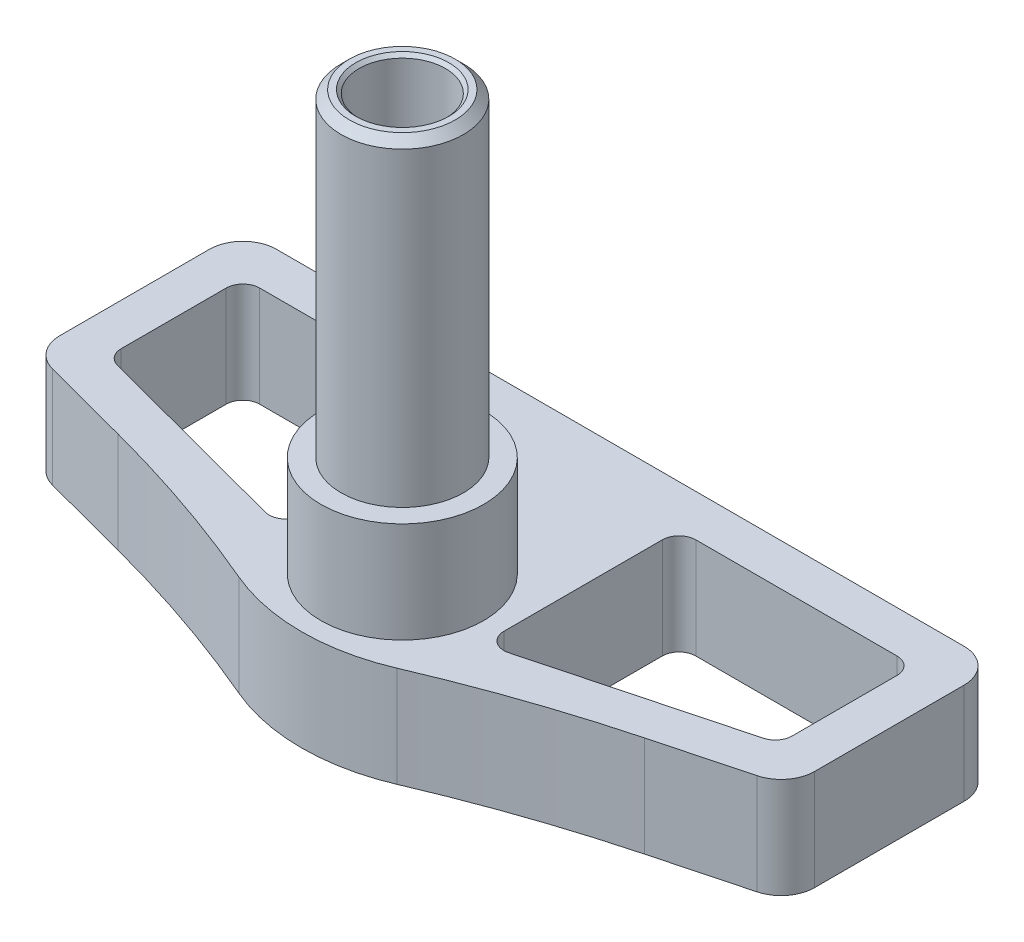
SolidWorks part; units mm, degrees
ref_plane "Front Plane" through (0, 0, 0) normal (0, 0, 1) x (1, 0, 0)
ref_plane "Top Plane" through (0, 0, 0) normal (0, 1, 0) x (1, 0, 0)
ref_plane "Right Plane" through (0, 0, 0) normal (1, 0, 0) x (0, 0, -1)
sketch "Sketch2" plane through (0, 0, 0) normal (0, 0, 1) x (1, 0, 0)
  line L1 (-12.5, 60) -> (12.5, 60)
  line L2 (-12.5, 60) -> (-12.5, 10)
  line L3 (-12.5, 10) -> (12.5, 10)
  line L4 (12.5, 60) -> (12.5, 10)
  line L5 (-22.5, 70) -> (22.5, 70)
  line L6 (-22.5, 70) -> (-22.5, 0)
  line L7 (-22.5, 0) -> (22.5, 0)
  line L8 (22.5, 70) -> (22.5, 0)
  point P4 (0, 10)
  point P10 (0, 0)
  dimension "D1" = 60
  dimension "D2" = 25
  dimension "D3" = 10
  dimension "D4" = 10
  dimension "D5" = 10
extrude "Boss-Extrude2" add sketch "Sketch2" along normal blind 10
sketch "Sketch3" plane through (0, 70, 0) normal (0, 1, 0) x (1, 0, 0)
  line L0 (-12, 0) -> (-12, -4)
  line L1 (22.5, 0) -> (-22.5, 0) construction
  line L2 (-12, -4) -> (-5, -4)
  line L3 (-5, -4) -> (-5, -8)
  line L4 (-5, -8) -> (5, -8)
  line L5 (5, -8) -> (5, -4)
  line L6 (5, -4) -> (12, -4)
  line L7 (12, -4) -> (12, 0)
  line L8 (-12, 0) -> (12, 0)
  point P4 (0, -8)
  dimension "D1" = 8
  dimension "D2" = 4
  dimension "D3" = 10
  dimension "D4" = 24
extrude "Cut-Extrude1" cut sketch "Sketch3" against normal up to next
sketch "Sketch4" plane through (0, 70, 0) normal (0, 1, 0) x (1, 0, 0)
  line L0 (-12, -10) -> (12, -10)
  line L1 (22.5, -10) -> (-22.5, -10) construction
  arc A0 (12, -10) -> (4.8, -15.4) centre (12, -17.5) ccw
  arc A1 (4.8, -15.4) -> (-4.8, -15.4) centre (0, -14) cw
  arc A2 (-4.8, -15.4) -> (-12, -10) centre (-12, -17.5) ccw
  circle A3 centre (0, -14) radius 3.65 construction
  dimension "D1" = 7.3
  dimension "D4" = 5
  dimension "D2" = 14
  dimension "D3" = 7.5
extrude "Boss-Extrude3" add sketch "Sketch4" against normal up to surface (10 mm away) up to face at (0, 60, 4.3333)
sketch "Sketch6" plane through (0, 70, 0) normal (0, 1, 0) x (1, 0, 0)
  circle A0 centre (0, -13) radius 3.65
  circle A1 centre (0, -13) radius 4.85 construction
  dimension "D1" = 7.3
  dimension "D2" = 9.7
  dimension "D3" = 13
extrude "Boss-Extrude4" add sketch "Sketch6" along normal blind 16
sketch "Sketch7" plane through (0, 0, 0) normal (0, -1, 0) x (1, 0, 0)
  line L1 (63, 1.7311) -> (15.6931, 14.2587) construction
  line L2 (-15.6931, 14.2587) -> (-63, 1.7311) construction
  line L3 (63, 1.7311) -> (15.6931, 14.2587) construction
  line L4 (-15.6931, 14.2587) -> (-63, 1.7311) construction
  line L5 (-22.5, 10) -> (-22.5, 12.4561)
  line L6 (-22.5, 12.4561) -> (-15.6931, 14.2587)
  line L7 (15.6931, 14.2587) -> (22.5, 12.4561)
  line L8 (22.5, 12.4561) -> (22.5, 10)
  line L9 (22.5, 10) -> (-22.5, 10)
  arc A6 (12.8214, 17.2181) -> (15.6931, 14.2587) centre (16.7171, 18.1254) ccw construction
  arc A7 (-15.6931, 14.2587) -> (-12.8214, 17.2181) centre (-16.7171, 18.1254) ccw construction
  arc A8 (12.8214, 17.2181) -> (15.6931, 14.2587) centre (16.7171, 18.1254) ccw construction
  arc A9 (-15.6931, 14.2587) -> (-12.8214, 17.2181) centre (-16.7171, 18.1254) ccw construction
  arc A11 (-15.6931, 14.2587) -> (-4.7143, 18.0352) centre (-36.2283, 91.8038) ccw
  arc A12 (-4.7143, 18.0352) -> (4.7143, 18.0352) centre (0, 7) cw
  arc A13 (4.7143, 18.0352) -> (15.6931, 14.2587) centre (36.2283, 91.8038) ccw
  dimension "D2" = 12
  dimension "D1" = 7
extrude "Boss-Extrude5" add sketch "Sketch7" against normal up to surface (10 mm away) up to face at (0, 10, 5)
sketch "Sketch8" plane through (0, 0, 0) normal (1, 0, 0) x (0, 0, -1)
  line L0 (-19, 70) -> (-19, 66.9) construction
  line L1 (-15.4, 70) -> (-19, 70) construction
  line L2 (-19, 60) -> (-19, 50.5) construction
  line L3 (-19, 60) -> (-15.4, 60) construction
  line L4 (-19, 66.9) -> (-23, 66.9)
  line L5 (-23, 66.9) -> (-23, 50.5)
  line L6 (-23, 50.5) -> (-19.5, 50.5)
  line L7 (-19.5, 50.5) -> (-10, 60)
  line L8 (-19, 70) -> (-19, 60) construction
  line L11 (-19, 66.9) -> (-10, 66.9)
  line L12 (-10, 60) -> (-10, 70) construction
  line L13 (-10, 66.9) -> (-10, 60)
  dimension "D1" = 9.5
  dimension "D2" = 3.1
  dimension "D3" = 45
  dimension "D5" = 4
extrude "Boss-Extrude8" add sketch "Sketch8" along normal mid plane 16
sketch "Sketch9" plane through (0, 0, 23) normal (0, 0, 1) x (1, 0, 0)
  line L0 (8, 66.9) -> (-8, 66.9) construction
  line L1 (-3, 66.9) -> (3, 66.9)
  line L2 (-3, 66.9) -> (-3, 50.5)
  line L3 (-3, 50.5) -> (3, 50.5)
  line L4 (3, 66.9) -> (3, 50.5)
  line L5 (8, 50.5) -> (-8, 50.5) construction
  point P8 (0, 50.5)
  dimension "D1" = 6
extrude "Cut-Extrude2" cut sketch "Sketch9" against normal blind 6
sketch "Sketch10" plane through (-8, 0, 0) normal (-1, 0, 0) x (0, 0, 1)
  line L0 (23, 50.5) -> (23, 66.9) construction
  line L1 (19.5, 50.5) -> (17, 53) construction
  line L2 (17, 53) -> (17, 66.9) construction
  line L3 (23, 50.5) -> (23, 66.9) construction
  line L4 (19.5, 50.5) -> (17, 53) construction
  line L5 (17, 53) -> (17, 66.9) construction
  line L6 (18.35, 64.4) -> (18.35, 54.4)
  line L7 (21.65, 54.4) -> (21.65, 64.4)
  line L8 (17, 59.95) -> (23, 59.95) construction
  line L9 (11.1557, 66.9) -> (23, 66.9) construction
  arc A0 (18.35, 54.4) -> (21.65, 54.4) centre (20, 54.4) ccw
  arc A1 (21.65, 64.4) -> (18.35, 64.4) centre (20, 64.4) ccw
  point P14 (20, 59.95)
  dimension "D1" = 3.3
  dimension "D2" = 10
  dimension "D3" = 2.5
extrude "Cut-Extrude3" cut sketch "Sketch10" against normal through all both and the other way through all
sketch "Sketch11" plane through (0, 10, 0) normal (0, 1, 0) x (1, 0, 0)
  line L1 (-32.1748, 6.5469) -> (31.625, 6.5469)
  line L2 (-32.1748, 6.5469) -> (-32.1748, -25.2398)
  line L3 (-32.1748, -25.2398) -> (31.625, -25.2398)
  line L4 (31.625, 6.5469) -> (31.625, -25.2398)
extrude "Cut-Extrude4" cut sketch "Sketch11" along normal through all
sketch "Sketch12" plane through (0, 10, 0) normal (0, 1, 0) x (1, 0, 0)
  circle A1 centre (0, -13) radius 3.65
  circle A2 centre (0, -13) radius 3.65
  dimension "D1" = 0
extrude "Boss-Extrude9" add sketch "Sketch12" along normal blind 21
sketch "Sketch13" plane through (0, 10, 0) normal (0, 1, 0) x (1, 0, 0)
  circle A0 centre (0, -13) radius 4.85
  circle A3 centre (0, -13) radius 3.65 construction
  circle A4 centre (0, -13) radius 3.65
  dimension "D2" = 9.7
extrude "Boss-Extrude10" add sketch "Sketch13" along normal blind 2
sketch "Sketch14" plane through (0, 10, 0) normal (0, 1, 0) x (1, 0, 0)
  line L5 (22.5, -12.4561) -> (22.5, 0)
  line L6 (22.5, 0) -> (-22.5, 0)
  line L7 (-22.5, 0) -> (-22.5, -12.4561)
  line L8 (-22.5, -12.4561) -> (-15.6931, -14.2587)
  line L9 (15.6931, -14.2587) -> (22.5, -12.4561)
  line L10 (22.5, -12.4561) -> (22.5, 0)
  line L11 (22.5, 0) -> (-22.5, 0)
  line L12 (-22.5, 0) -> (-22.5, -12.4561)
  line L13 (-22.5, -12.4561) -> (-15.6931, -14.2587)
  line L14 (15.6931, -14.2587) -> (22.5, -12.4561)
  circle A0 centre (0, -13) radius 4.85 construction
  circle A1 centre (0, -13) radius 4.85
  arc A3 (-4.7143, -18.0352) -> (-15.6931, -14.2587) centre (-36.2283, -91.8038) ccw
  arc A4 (-4.7143, -18.0352) -> (4.7143, -18.0352) centre (0, -7) ccw
  arc A5 (15.6931, -14.2587) -> (4.7143, -18.0352) centre (36.2283, -91.8038) ccw
  arc A6 (-4.7143, -18.0352) -> (-15.6931, -14.2587) centre (-36.2283, -91.8038) ccw
  arc A7 (-4.7143, -18.0352) -> (4.7143, -18.0352) centre (0, -7) ccw
  arc A8 (15.6931, -14.2587) -> (4.7143, -18.0352) centre (36.2283, -91.8038) ccw
  dimension "D1" = 0
extrude "Cut-Extrude6" cut sketch "Sketch14" against normal blind 4
sketch "Sketch15" plane through (0, 6, 0) normal (0, 1, 0) x (1, 0, 0)
  line L0 (6, -2.5) -> (20, -2.5)
  line L1 (20, -2.5) -> (20, -10.532)
  line L2 (20, -10.532) -> (6, -14.2394)
  line L3 (6, -14.2394) -> (6, -2.5)
  line L4 (0, 0) -> (0, -19) construction
  line L5 (22.5, 0) -> (-22.5, 0) construction
  line L6 (-6, -14.2394) -> (-6, -2.5)
  line L7 (-20, -10.532) -> (-6, -14.2394)
  line L8 (-20, -2.5) -> (-20, -10.532)
  line L9 (-6, -2.5) -> (-20, -2.5)
  line L10 (-20, -2.5) -> (-20, 0) construction
  line L11 (-20, -2.5) -> (-22.5, -2.5) construction
  line L12 (-22.5, 0) -> (-22.5, -12.4561) construction
  line L13 (-20, -10.532) -> (-20.64, -12.9487) construction
  line L14 (-22.5, -12.4561) -> (-15.6931, -14.2587) construction
  arc A0 (-4.7143, -18.0352) -> (4.7143, -18.0352) centre (0, -7) ccw construction
  dimension "D1" = 2.5
  dimension "D2" = 12
extrude "Cut-Extrude7" cut sketch "Sketch15" against normal through all
fillet "Fillet1" radius 1 8 edges at (-20, 3, 2.5) (-6, 3, 14.2394) (-20, 3, 10.532) (6, 3, 14.2394) (6, 3, 2.5) (20, 3, 2.5) (20, 3, 10.532) (-6, 3, 2.5)
sketch "Sketch16" plane through (0, 31, 0) normal (0, 1, 0) x (1, 0, 0)
  circle A0 centre (0, -13) radius 2.575
  dimension "D1" = 5.15
extrude "Cut-Extrude8" cut sketch "Sketch16" against normal blind 13.5
chamfer "Chamfer1" distance 0.5 angle 45 1 edges at (0, 31, 16.65)
chamfer "Chamfer2" distance 0.2 angle 45 1 edges at (0, 31, 15.575)
sketch "Sketch17" plane through (0, 17.5, 0) normal (0, 1, 0) x (1, 0, 0)
  circle A0 centre (0, -13) radius 2.575 construction
  circle A1 centre (0, -13) radius 2.575 construction
  circle A2 centre (0, -13) radius 2.4
  dimension "D1" = 4.8
extrude "Cut-Extrude9" cut sketch "Sketch17" against normal blind 12
fillet "Fillet2" radius 2 4 edges at (-22.5, 3, 0) (-22.5, 3, 12.4561) (22.5, 3, 12.4561) (22.5, 3, 0)
